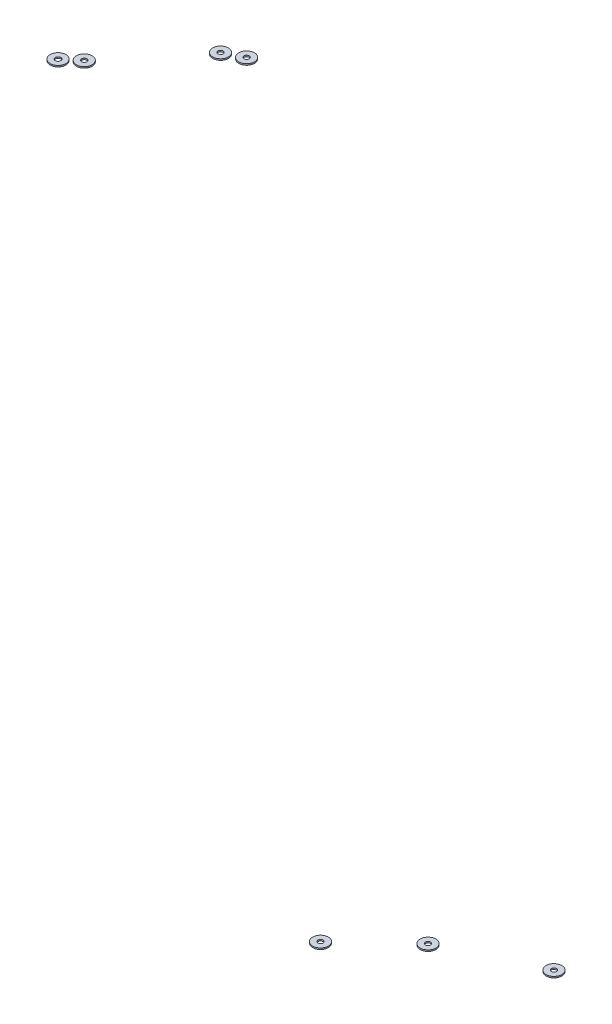
SolidWorks part; units mm, degrees
ref_plane "Płaszczyzna XY" through (0, 0, 0) normal (0, 0, 1) x (1, 0, 0)
ref_plane "Płaszczyzna XZ" through (0, 0, 0) normal (0, 1, 0) x (1, 0, 0)
ref_plane "Płaszczyzna YZ" through (0, 0, 0) normal (1, 0, 0) x (0, 0, -1)
sketch "Szkic1" plane through (0, 705.3, 0) normal (0, 1, 0) x (1, 0, 0)
  circle A0 centre (-421.0901, -327.7251) radius 1.5
  circle A1 centre (-431.0397, -332.7742) radius 1.5
  circle A2 centre (-466.3081, -375.8594) radius 1.5
  circle A3 centre (-474.4492, -382.7937) radius 1.6059
  circle A4 centre (-421.0901, -327.7251) radius 4.5
  circle A5 centre (-431.0397, -332.7742) radius 4.5
  circle A6 centre (-466.3081, -375.8594) radius 4.5
  circle A7 centre (-474.4492, -382.7937) radius 4.5
  dimension "D1" = 9
  dimension "D2" = 9
  dimension "D3" = 9
  dimension "D4" = 9
extrude "Dodanie-wyciągnięcie1" add sketch "Szkic1" along normal blind 0.8
sketch "Szkic2" plane through (0, 294.7, 0) normal (0, -1, 0) x (1, 0, 0)
  circle A0 centre (-289.6871, 282.4241) radius 1.5
  circle A1 centre (-339.083, 305.4298) radius 1.5
  circle A2 centre (-370.9569, 335.3671) radius 1.5
  circle A3 centre (-370.9569, 335.3671) radius 4.5
  circle A4 centre (-339.083, 305.4298) radius 4.5
  circle A5 centre (-289.6871, 282.4241) radius 4.5
  dimension "D1" = 9
  dimension "D2" = 9
  dimension "D3" = 9
extrude "Dodanie-wyciągnięcie2" add sketch "Szkic2" along normal blind 0.8 separate body
